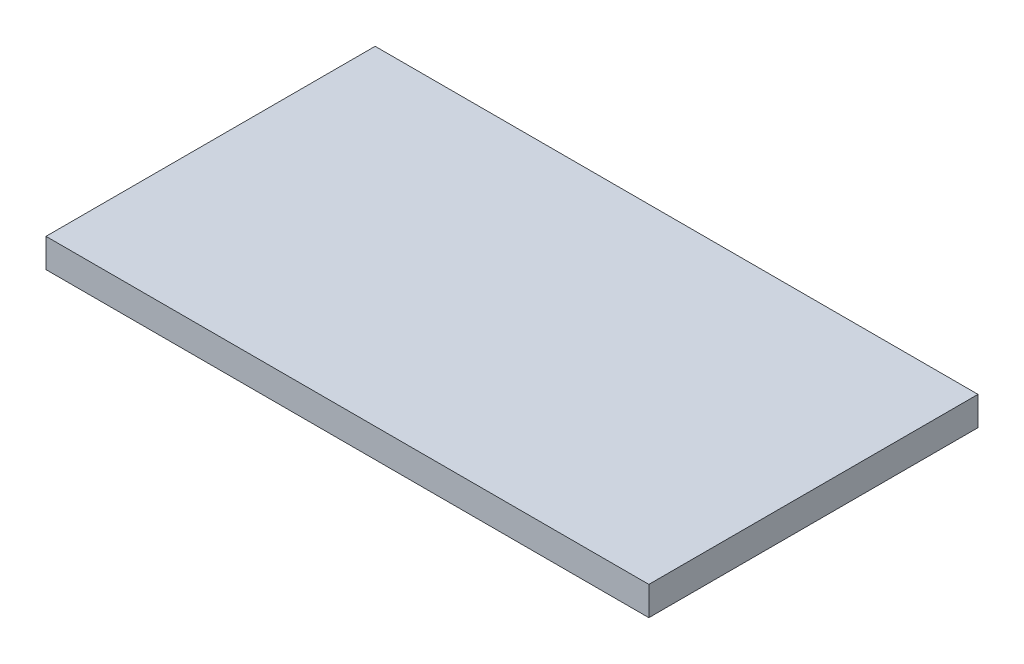
SolidWorks part; units mm, degrees
material "Custom Plastic"
ref_plane "Front Plane" through (0, 0, 0) normal (0, 0, 1) x (1, 0, 0)
ref_plane "Top Plane" through (0, 0, 0) normal (0, 1, 0) x (1, 0, 0)
ref_plane "Right Plane" through (0, 0, 0) normal (1, 0, 0) x (0, 0, -1)
sketch "Sketch1" plane through (0, 0, 0) normal (0, 1, 0) x (1, 0, 0)
  line L0 (-35.9391, 2.55) -> (38.4915, 2.55) construction
  line L1 (-26.1, -11.7) -> (26.1, -11.7)
  line L2 (-26.1, -11.7) -> (-26.1, 16.8)
  line L3 (-26.1, 16.8) -> (26.1, 16.8)
  line L4 (26.1, -11.7) -> (26.1, 16.8)
  line L5 (-26.1, -11.7) -> (26.1, 16.8) construction
  line L6 (-26.1, 16.8) -> (26.1, -11.7) construction
  line L7 (0, 29.6091) -> (0, -31.2199) construction
  line L8 (0, 16.8) -> (0, 0) construction
  line L10 (-17.6603, -1.9) -> (17.6603, -1.9)
  line L11 (-17.6603, 7) -> (17.6603, 7)
  line L12 (-17.6603, 7) -> (-17.6603, 12.8)
  line L13 (-17.6603, 12.8) -> (17.6603, 12.8)
  line L14 (17.6603, 7) -> (17.6603, 12.8)
  line L23 (17.6603, -1.9) -> (17.6603, -7.7)
  line L24 (-17.6603, -7.7) -> (17.6603, -7.7)
  line L25 (-17.6603, -1.9) -> (-17.6603, -7.7)
  circle A0 centre (-22.8, -3.2) radius 1
  circle A1 centre (22.8, -3.2) radius 1
  circle A2 centre (22.8, 8.3) radius 1
  circle A3 centre (-22.8, 8.3) radius 1
  point P0 (0, 0)
  dimension "D3" = 2
  dimension "D1" = 28.5
  dimension "D2" = 52.2
  dimension "D4" = 8.5
  dimension "D5" = 8.5
  dimension "D7" = 4
  dimension "D9" = 5.8
  dimension "D10" = 35.3206
  dimension "D11" = 8.4397
extrude "Boss-Extrude1" add sketch "Sketch1" along normal blind 2.5
sketch "Sketch2" plane through (0, 0, 0) normal (0, -1, 0) x (1, 0, 0)
  line L4 (26.1, -16.8) -> (26.1, 11.7)
  line L5 (26.1, 11.7) -> (-26.1, 11.7)
  line L6 (-26.1, 11.7) -> (-26.1, -16.8)
  line L7 (-26.1, -16.8) -> (26.1, -16.8)
  line L8 (26.1, -16.8) -> (26.1, 11.7)
  line L9 (26.1, 11.7) -> (-26.1, 11.7)
  line L10 (-26.1, 11.7) -> (-26.1, -16.8)
  line L11 (-26.1, -16.8) -> (26.1, -16.8)
  dimension "D1" = 0
extrude "Boss-Extrude2" add sketch "Sketch2" against normal up to surface (2.5 mm away) up to face at (0, 2.5, -9.9)
